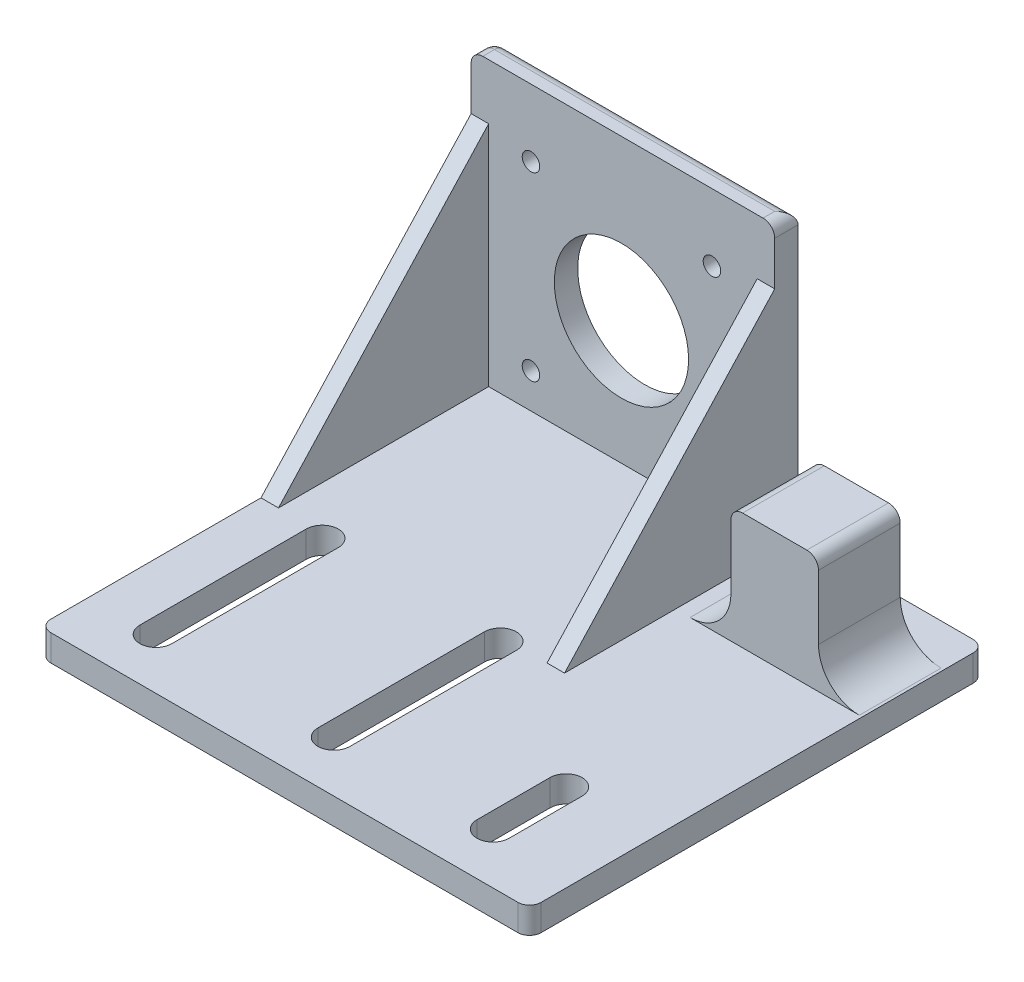
SolidWorks part; units mm, degrees
ref_plane "Front Plane" through (0, 0, 0) normal (0, 0, 1) x (1, 0, 0)
ref_plane "Top Plane" through (0, 0, 0) normal (0, 1, 0) x (1, 0, 0)
ref_plane "Right Plane" through (0, 0, 0) normal (1, 0, 0) x (0, 0, -1)
sketch "Sketch1" plane through (0, 0, 0) normal (0, 1, 0) x (1, 0, 0)
  line L0 (42, -54) -> (42, 24)
  line L1 (-42, -54) -> (42, -54)
  line L2 (-42, -54) -> (-42, 24)
  line L3 (-42, 24) -> (42, 24)
  dimension "D1" = 78
  dimension "D2" = 24
  dimension "D3" = 84
  dimension "D4" = 42
extrude "Boss-Extrude1" add sketch "Sketch1" along normal blind 4.5
fillet "Fillet2" radius 2 4 edges at (-42, 2.25, -24) (42, 2.25, -24) (42, 2.25, 54) (-42, 2.25, 54)
sketch "Sketch2" plane through (0, 4.5, 0) normal (0, 1, 0) x (1, 0, 0)
  line L0 (-42, 22) -> (-42, -52) construction
  line L5 (40, 24) -> (-40, 24) construction
  line L6 (-40, -54) -> (40, -54) construction
  line L8 (-33.5, -16.75) -> (-33.5, -45.25)
  line L10 (-28, -16.75) -> (-28, -45.25)
  line L11 (-15.5, 46.6682) -> (-15.5, -25.2267) construction
  line L12 (2.5, -16.75) -> (2.5, -45.25)
  line L13 (-3, -16.75) -> (-3, -45.25)
  arc A0 (2.5, -45.25) -> (-3, -45.25) centre (-0.25, -45.25) cw
  arc A1 (-33.5, -45.25) -> (-28, -45.25) centre (-30.75, -45.25) ccw
  arc A4 (-28, -16.75) -> (-33.5, -16.75) centre (-30.75, -16.75) ccw
  arc A5 (-3, -16.75) -> (2.5, -16.75) centre (-0.25, -16.75) cw
  dimension "D5" = 5.5
  dimension "D6" = 8.75
  dimension "D8" = 2.75
  dimension "D9" = 2.75
  dimension "D11" = 15.25
  dimension "D4" = 28.5
  dimension "D7" = 11.25
  dimension "D10" = 5.5
extrude "Cut-Extrude1" cut sketch "Sketch2" against normal through all and the other way through all
sketch "Sketch3" plane through (0, 4.5, 0) normal (0, 1, 0) x (1, 0, 0)
  line L0 (-42, 22) -> (-42, -52) construction
  line L1 (-42, 20) -> (10, 20)
  line L2 (-42, 20) -> (-42, 22)
  line L3 (-40, 24) -> (10, 24)
  line L4 (10, 20) -> (10, 24)
  line L5 (40, 24) -> (-40, 24) construction
  arc A2 (-40, 24) -> (-42, 22) centre (-40, 22) ccw
  arc A3 (-40, 24) -> (-42, 22) centre (-40, 22) ccw
  dimension "D1" = 50
  dimension "D2" = 4
  dimension "D3" = 0
extrude "Boss-Extrude2" add sketch "Sketch3" along normal blind 48.5
fillet "Fillet4" radius 2 4 edges at (-15, 53, -24) (-41.4142, 53, -23.4142) (10, 53, -22) (-42, 53, -21)
sketch "Sketch4" plane through (-42, 0, 0) normal (-1, 0, 0) x (0, 0, 1)
  line L0 (16, 4.5) -> (-20, 43.5)
  line L1 (-20, 4.5) -> (52, 4.5) construction
  line L2 (-20, 51) -> (-20, 4.5) construction
  dimension "D1" = 7.5
rib "Rib7" sketch "Sketch4" sketch "Sketch4" thickness 3 extrusion direction parallel to sketch draft on no parameters "D1"=3
sketch "Sketch6" plane through (10, 0, 0) normal (1, 0, 0) x (0, 0, -1)
  line L0 (20, 43.5) -> (-16, 4.5)
rib "Rib8" sketch "Sketch6" sketch "Sketch6" thickness 3 extrusion direction parallel to sketch draft on no parameters "D1"=3
sketch "Sketch7" plane through (0, 0, -20) normal (0, 0, 1) x (1, 0, 0)
  line L0 (-16.25, 58.1041) -> (-16.25, -5.9394) construction
  line L1 (-39, 4.5) -> (-39, 43.5) construction
  line L3 (-40, 53) -> (8, 53) construction
  circle A0 centre (-16.25, 25.65) radius 11.5
  circle A1 centre (-31.75, 41.5) radius 1.5
  circle A2 centre (-31.75, 10.5) radius 1.5
  circle A3 centre (-0.75, 10.5) radius 1.5
  circle A4 centre (-0.75, 41.5) radius 1.5
  dimension "D2" = 27.35
  dimension "D3" = 23
  dimension "D4" = 3
  dimension "D5" = 3
  dimension "D1" = 22.75
  dimension "D6" = 31
  dimension "D7" = 11.5
  dimension "D8" = 15.5
extrude "Cut-Extrude2" cut sketch "Sketch7" against normal through all
sketch "Sketch8" plane through (0, 4.5, 0) normal (0, 1, 0) x (1, 0, 0)
  line L0 (42, -52) -> (42, 22) construction
  line L1 (19.5, 17) -> (34.5, 17)
  line L2 (19.5, 17) -> (19.5, 3)
  line L3 (19.5, 3) -> (34.5, 3)
  line L4 (34.5, 17) -> (34.5, 3)
  line L5 (40, 24) -> (10, 24) construction
  dimension "D1" = 15
  dimension "D2" = 14
  dimension "D3" = 7.5
  dimension "D4" = 7
extrude "Boss-Extrude3" add sketch "Sketch8" along normal blind 20
fillet "Fillet5" radius 7 2 edges at (34.5, 4.5, -10) (19.5, 4.5, -10)
fillet "Fillet6" radius 2 2 edges at (19.5, 24.5, -10) (34.5, 24.5, -10)
sketch "Sketch9" plane through (0, 0, -17) normal (0, 0, -1) x (-1, 0, 0)
  line L0 (-27, 51.8073) -> (-27, -6.5478) construction
  line L3 (-32.5, 24.5) -> (-21.5, 24.5) construction
  line L5 (-19.5, 22.5) -> (-19.5, 11.5) construction
  circle A0 centre (-27, 16.5) radius 4
  dimension "D1" = 8
  dimension "D3" = 8
  dimension "D2" = 7.5
extrude "Cut-Extrude3" cut sketch "Sketch9" against normal blind 10
sketch "Sketch10" plane through (0, 4.5, 0) normal (0, 1, 0) x (1, 0, 0)
  line L0 (-40, -54) -> (40, -54) construction
  line L2 (24.25, -32.75) -> (24.25, -45.25)
  line L4 (29.75, -32.75) -> (29.75, -45.25)
  line L5 (32.5, 3) -> (32.5, 17) construction
  arc A0 (24.25, -45.25) -> (29.75, -45.25) centre (27, -45.25) ccw
  arc A1 (29.75, -32.75) -> (24.25, -32.75) centre (27, -32.75) ccw
  dimension "D2" = 8.75
  dimension "D3" = 2.75
  dimension "D5" = 2.75
  dimension "D1" = 5.5
  dimension "D4" = 12.5
  dimension "D6" = 2.75
extrude "Cut-Extrude4" cut sketch "Sketch10" against normal through all
